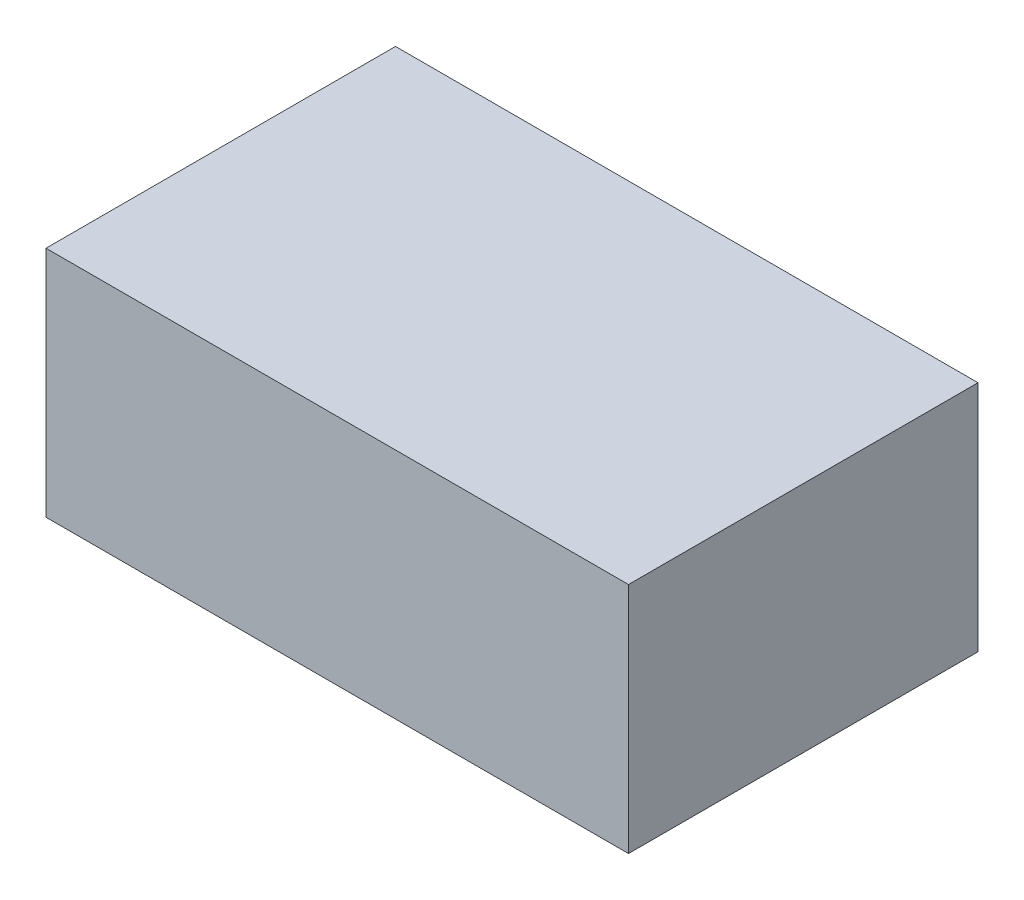
SolidWorks part; units mm, degrees
ref_plane "Front Plane" through (0, 0, 0) normal (0, 0, 1) x (1, 0, 0)
ref_plane "Top Plane" through (0, 0, 0) normal (0, 1, 0) x (1, 0, 0)
ref_plane "Right Plane" through (0, 0, 0) normal (1, 0, 0) x (0, 0, -1)
sketch "Sketch1" plane through (0, 0, 0) normal (0, 1, 0) x (1, 0, 0)
  line L1 (30, -18) -> (-30, -18)
  line L2 (30, -18) -> (30, 18)
  line L3 (30, 18) -> (-30, 18)
  line L4 (-30, -18) -> (-30, 18)
  line L5 (30, -18) -> (-30, 18) construction
  line L6 (30, 18) -> (-30, -18) construction
  point P0 (0, 0)
  dimension "D1" = 60
  dimension "D2" = 36
extrude "Boss-Extrude1" add sketch "Sketch1" against normal blind 24
